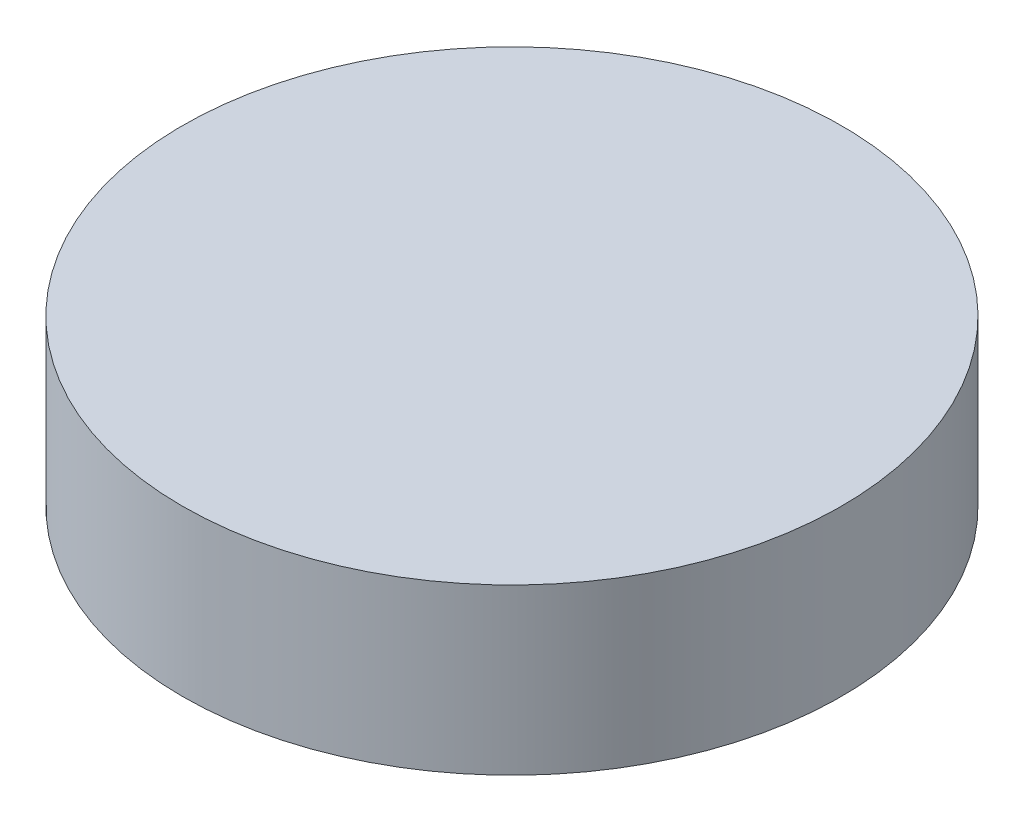
SolidWorks part; units mm, degrees
ref_plane "Front Plane" through (0, 0, 0) normal (0, 0, 1) x (1, 0, 0)
ref_plane "Top Plane" through (0, 0, 0) normal (0, 1, 0) x (1, 0, 0)
ref_plane "Right Plane" through (0, 0, 0) normal (1, 0, 0) x (0, 0, -1)
sketch "Sketch1" plane through (0, 0, 0) normal (0, 1, 0) x (1, 0, 0)
  circle A0 centre (0, 0) radius 20
  dimension "D1" = 40
extrude "Boss-Extrude1" add sketch "Sketch1" along normal blind 10
